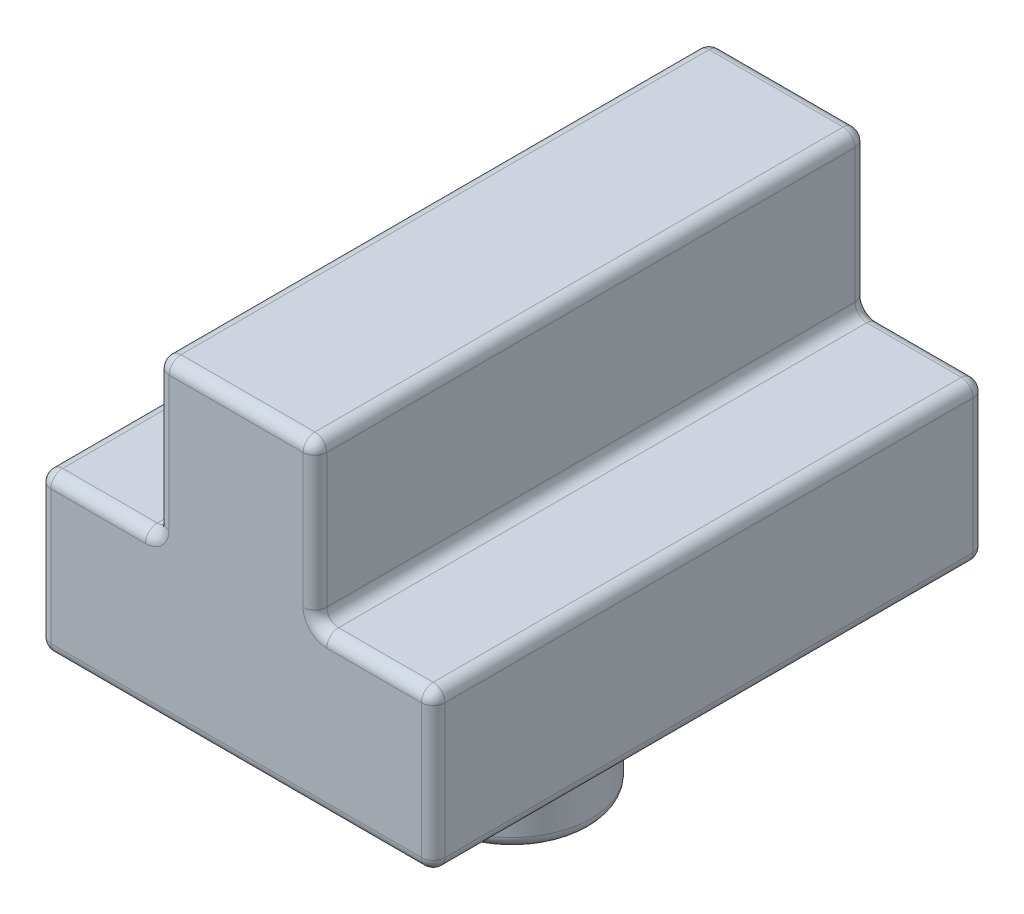
SolidWorks part; units mm, degrees
ref_plane "Front Plane" through (0, 0, 0) normal (0, 0, 1) x (1, 0, 0)
ref_plane "Top Plane" through (0, 0, 0) normal (0, 1, 0) x (1, 0, 0)
ref_plane "Right Plane" through (0, 0, 0) normal (1, 0, 0) x (0, 0, -1)
sketch "Sketch1" plane through (0, 0, 0) normal (0, 0, 1) x (1, 0, 0)
  line L0 (0, 0) -> (0, 20)
  line L1 (0, 20) -> (15, 20)
  line L2 (15, 20) -> (15, 40)
  line L3 (15, 40) -> (35, 40)
  line L4 (35, 40) -> (35, 20)
  line L5 (35, 20) -> (50, 20)
  line L6 (50, 20) -> (50, 0)
  line L7 (50, 0) -> (0, 0)
  dimension "D1" = 20
  dimension "D2" = 15
  dimension "D3" = 20
  dimension "D4" = 20
extrude "Boss-Extrude1" add sketch "Sketch1" along normal mid plane 70
sketch "Sketch2" plane through (0, 0, 0) normal (0, -1, 0) x (-1, 0, 0)
  circle A0 centre (-25, 0) radius 10
  dimension "D1" = 20
  dimension "D2" = 25
  dimension "D3" = 35
extrude "Boss-Extrude2" add sketch "Sketch2" along normal blind 20
fillet "Fillet1" radius 1.5 25 edges at (7.5, 20, 35) (15, 30, 35) (15, 20, 0) (25, 40, 35) (15, 40, 0) (35, 30, 35) (35, 40, 0) (42.5, 20, 35) (35, 20, 0) (42.5, 20, -35) (35, 30, -35) (25, 40, -35) (15, 30, -35) (7.5, 20, -35) (0, 20, 0) (0, 10, 35) (0, 10, -35) (50, 10, 35) (50, 20, 0) (50, 10, -35) (0, 0, 0) (25, 0, 35) (50, 0, 0) (25, 0, -35) (35, 0, 0)
fillet "Fillet2" radius 1.5 1 edges at (35, -20, 0)
